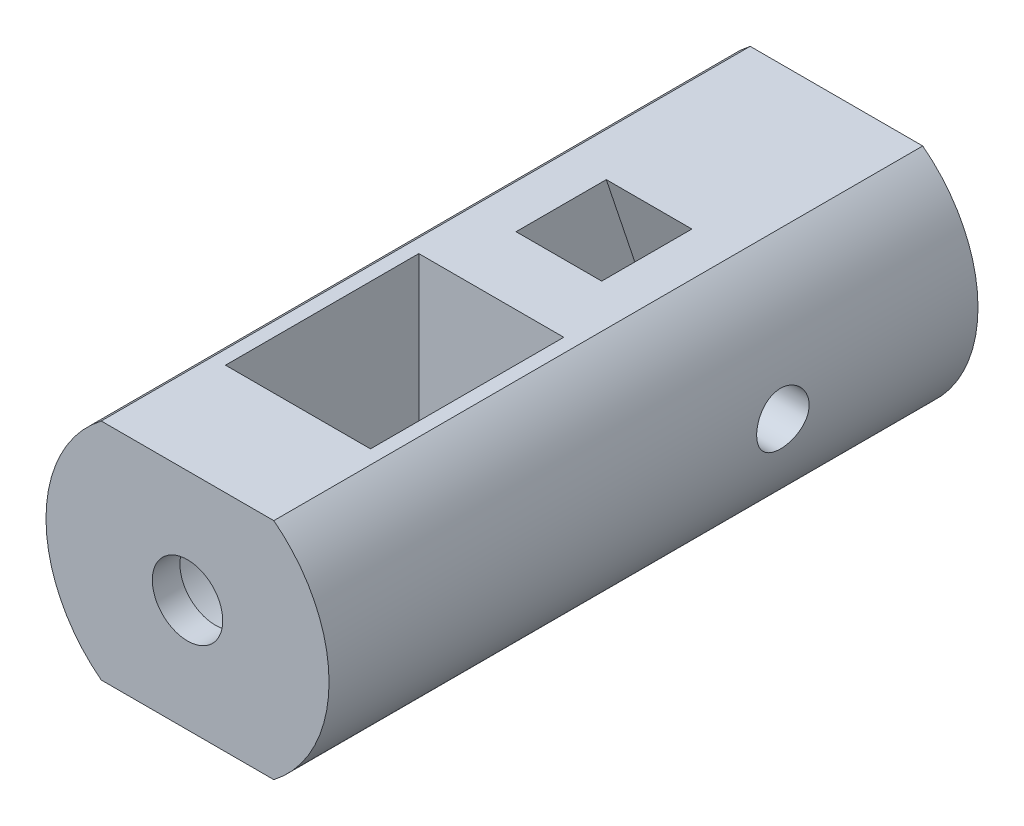
SolidWorks part; units mm, degrees
material "ABS"
ref_plane "Alzado" through (0, 0, 0) normal (0, 0, 1) x (1, 0, 0)
ref_plane "Planta" through (0, 0, 0) normal (0, 1, 0) x (1, 0, 0)
ref_plane "Vista lateral" through (0, 0, 0) normal (1, 0, 0) x (0, 0, -1)
ref_plane "Plano1" through (0, 0, 117.639) normal (0, 0, -1) x (-1, 0, 0)
sketch "Croquis1" plane through (0, 0, 117.639) normal (0, 0, -1) x (-1, 0, 0)
  line L0 (-6.25, 309.2797) -> (6.25, 309.2797)
  line L1 (6.25, 325.5278) -> (-6.25, 325.5278)
  arc A0 (-6.25, 325.5278) -> (-6.25, 309.2797) centre (0, 317.4037) ccw
  arc A1 (6.25, 309.2797) -> (6.25, 325.5278) centre (0, 317.4037) ccw
extrude "Saliente-Extruir1" add sketch "Croquis1" against normal blind 47
sketch "Croquis2" plane through (0, 325.5278, 0) normal (0, 1, 0) x (-1, 0, 0)
  line L0 (3.1, 132.3284) -> (-3.1, 132.3284)
  line L1 (-3.1, 132.3284) -> (-3.1, 125.793)
  line L2 (-3.1, 125.793) -> (3.1, 125.793)
  line L3 (3.1, 125.793) -> (3.1, 132.3284)
extrude "Cortar-Extruir1" cut sketch "Croquis2" against normal through all
sketch "Croquis3" plane through (0, 309.2797, 0) normal (0, -1, 0) x (1, 0, 0)
  line L0 (-5.25, 142.639) -> (5.25, 142.639)
  line L1 (5.25, 142.639) -> (5.25, 156.639)
  line L2 (5.25, 156.639) -> (-5.25, 156.639)
  line L3 (-5.25, 156.639) -> (-5.25, 142.639)
extrude "Cortar-Extruir2" cut sketch "Croquis3" against normal through all
draft "Ángulo de salida1" type of draft neutral plane draft angle 18.435 faces to draft 1 face at (0, 317.4037, 125.793) neutral plane through (6.25, 309.2797, 164.639) neutral plane normal (0, -1, 0) parameters "D1"=18.435
draft "Ángulo de salida2" type of draft neutral plane draft angle 18.435 faces to draft 1 face at (0, 317.4037, 132.3284) neutral plane through (6.25, 309.2797, 164.639) neutral plane normal (0, -1, 0) reverse direction yes parameters "D1"=18.435
hole_wizard "Taladro1" positions "Croquis5" profile "Croquis4" legacy
sketch "Croquis5" plane through (0, 0, 156.639) normal (0, 0, -1) x (-1, 0, 0)
  point P0 (0, 317.4037)
sketch "Croquis4" plane through (0, 317.4037, 156.639) normal (1, 0, 0) x (0, 1, 0)
  line L0 (0, 0) -> (0, 8)
  line L1 (0, 8) -> (2.55, 8)
  line L2 (2.55, 8) -> (2.55, 6)
  line L3 (2.55, 6) -> (5.25, 6)
  line L4 (5.25, 6) -> (5.25, 0)
  line L5 (5.25, 0) -> (0, 0)
  line L6 (0, 110) -> (0, -10) construction
  dimension "Diámetro" = 5.1
  dimension "Profundidad" = 8
  dimension "Diámetro de refrentado 1" = 10.5
  dimension "Profundidad de refrentado 1" = 6
hole_wizard "Diámetro de taladro Ø3.8 (3.8)1" positions "Croquis7" profile "Croquis6" hole size "Ø3.8" standard "Ansi Metric"
sketch "Croquis7" plane through (3.1, 0, 0) normal (-1, 0, 0) x (0, 0, 1)
  point P0 (131.7687, 317.4037)
sketch "Croquis6" plane through (3.1, 317.4037, 131.7687) normal (0, 1, 0) x (0, 0, 1)
  line L0 (0, 0) -> (0, 7.15)
  line L1 (0, 7.15) -> (1.9, 7.15)
  line L2 (1.9, 7.15) -> (1.9, 0)
  line L5 (1.9, 0) -> (0, 0)
  line L11 (0, -6.35) -> (0, 107.95) construction
  dimension "Diámetro de taladro hasta el siguiente" = 3.8
  dimension "Profundidad de taladro hasta el siguiente" = 7.15
hole_wizard "Diámetro de taladro Ø3.8 (3.8)2" positions "Croquis9" profile "Croquis8" hole size "Ø3.8" standard "Ansi Metric"
sketch "Croquis9" plane through (-3.1, 0, 0) normal (1, 0, 0) x (0, 0, -1)
  point P0 (-131.7687, 317.4037)
sketch "Croquis8" plane through (-3.1, 317.4037, 131.7687) normal (0, 1, 0) x (0, 0, -1)
  line L0 (0, 0) -> (0, 7.15)
  line L1 (0, 7.15) -> (1.9, 7.15)
  line L2 (1.9, 7.15) -> (1.9, 0)
  line L5 (1.9, 0) -> (0, 0)
  line L11 (0, -6.35) -> (0, 107.95) construction
  dimension "Diámetro de taladro hasta el siguiente" = 3.8
  dimension "Profundidad de taladro hasta el siguiente" = 7.15
